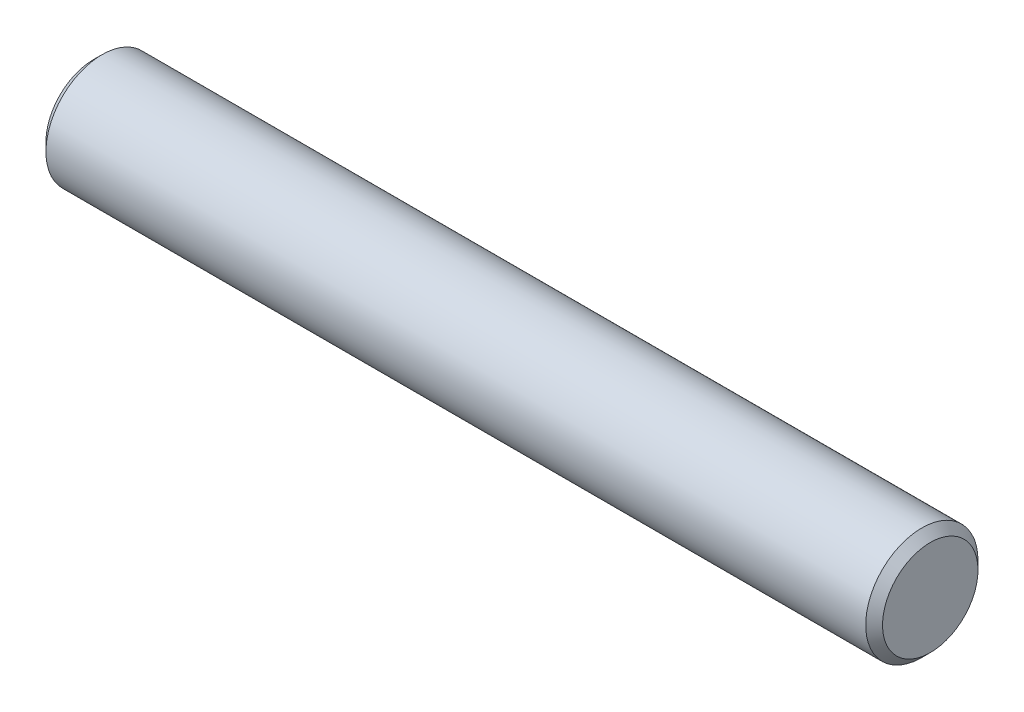
SolidWorks part; units mm, degrees
material "AISI 321 Annealed Stainless Steel (SS)"
ref_plane "Front Plane" through (0, 0, 0) normal (0, 0, 1) x (1, 0, 0)
ref_plane "Top Plane" through (0, 0, 0) normal (0, 1, 0) x (1, 0, 0)
ref_plane "Right Plane" through (0, 0, 0) normal (1, 0, 0) x (0, 0, -1)
sketch "Sketch1" plane through (0, 0, 0) normal (1, 0, 0) x (0, 0, -1)
  circle A0 centre (0, 0) radius 1
  dimension "D1" = 2
extrude "Boss-Extrude1" add sketch "Sketch1" along normal mid plane 14.9
chamfer "Chamfer1" distance 0.15 angle 45 2 edges at (7.45, 0, -1) (-7.45, 0, -1)
